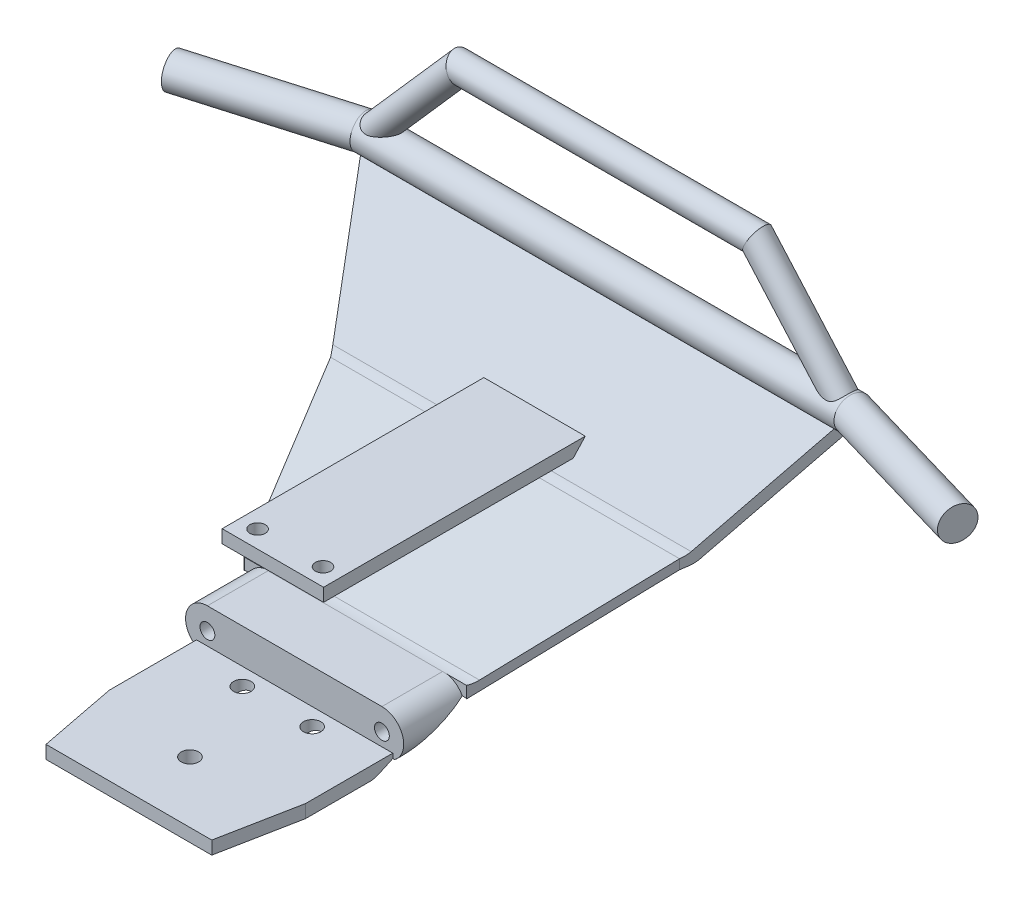
SolidWorks part; units mm, degrees
ref_plane "Front Plane" through (0, 0, 0) normal (0, 0, 1) x (1, 0, 0)
ref_plane "Top Plane" through (0, 0, 0) normal (0, 1, 0) x (1, 0, 0)
ref_plane "Right Plane" through (0, 0, 0) normal (1, 0, 0) x (0, 0, -1)
sketch "Sketch2" plane through (0, 0, 0) normal (1, 0, 0) x (0, 0, -1)
  line L0 (0, 0) -> (32.7095, 0)
  line L1 (34.7929, 0.4547) -> (87.4317, 24.5817)
  line L2 (89.0248, 25.7382) -> (111.3878, 50)
  line L3 (0, 0) -> (0, 3)
  line L4 (0, 3) -> (38, 3)
  line L5 (38, 3) -> (38, 11)
  line L6 (87.8264, 27.389) -> (109.9172, 51.3555)
  line L7 (38, 11) -> (51.9087, 11)
  line L8 (53.992, 11.4547) -> (86.2333, 26.2325)
  line L9 (109.9172, 51.3555) -> (111.3878, 50)
  arc A0 (51.9087, 11) -> (53.992, 11.4547) centre (51.9087, 16) ccw
  arc A1 (86.2333, 26.2325) -> (87.8264, 27.389) centre (84.15, 30.7778) ccw
  arc A2 (87.4317, 24.5817) -> (89.0248, 25.7382) centre (85.3484, 29.127) ccw
  arc A3 (32.7095, 0) -> (34.7929, 0.4547) centre (32.7095, 5) ccw
  point P17 (53, 11)
  point P22 (88.3444, 25)
  point P25 (33.8008, 0)
  dimension "D11" = 5
  dimension "D1" = 8
  dimension "D2" = 3
  dimension "D3" = 60
  dimension "D4" = 34
  dimension "D5" = 2
  dimension "D6" = 2
  dimension "D7" = 25
  dimension "D8" = 50
  dimension "D9" = 38
  dimension "D10" = 15
extrude "Boss-Extrude1" add sketch "Sketch2" along normal mid plane 114
sketch "Sketch18" plane through (0, 3, 0) normal (0, 1, 0) x (1, 0, 0)
  line L0 (0, 0) -> (0, 53.992) construction
  line L1 (57, 0) -> (-57, 0) construction
  line L2 (57, 53.992) -> (-57, 53.992) construction
  circle A0 centre (-8, 34) radius 2
  circle A1 centre (8, 34) radius 2
  circle A2 centre (0, 14) radius 2
  dimension "D3" = 4
  dimension "D4" = 4
  dimension "D5" = 4
  dimension "D1" = 14
  dimension "D2" = 34
  dimension "D6" = 8
  dimension "D7" = 8
extrude "Cut-Extrude3" cut sketch "Sketch18" against normal up to surface (3 mm away) up to face at (0, 0, -16.3548)
ref_plane "Plane2" through (0, 0, -38) normal (0, 0, 1) x (1, 0, 0)
sketch "Sketch19" plane through (0, 0, -38) normal (0, 0, 1) x (1, 0, 0)
  line L0 (0, 0) -> (0, 79.2721) construction
  line L1 (57, 0) -> (-57, 0) construction
  line L2 (-11.625, 30) -> (-11.625, 33)
  line L3 (-11.625, 33) -> (11.625, 33)
  line L4 (57, 0) -> (-57, 0) construction
  line L5 (-11.625, 30) -> (11.625, 30)
  line L8 (11.625, 33) -> (11.625, 30)
  line L9 (-11.625, 31.5) -> (17.3718, 31.5) construction
  point P13 (0, 30)
  dimension "D1" = 23.25
  dimension "D2" = 33
  dimension "D6" = 3
sketch "Sketch23" plane through (0, 0, 0) normal (0, 1, 0) x (1, 0, 0)
  line L0 (19, 0) -> (22.5, 18)
  line L1 (57, 0) -> (-57, 0) construction
  line L2 (22.5, 18) -> (22.5, 38)
  line L3 (22.5, 38) -> (25.5, 38)
  line L4 (25.5, 38) -> (25.5, 51.9087)
  line L5 (25.5, 51.9087) -> (40, 86.2333)
  line L6 (40, 86.2333) -> (57, 111.3878)
  line L7 (57, 111.3878) -> (57, 0)
  line L8 (57, 0) -> (19, 0)
  line L9 (57, 38) -> (-57, 38) construction
  line L10 (57, 51.9087) -> (-57, 51.9087) construction
  line L11 (57, 86.2333) -> (-57, 86.2333) construction
  line L12 (0, 0) -> (0, 127.1657) construction
  line L13 (-57, 0) -> (-19, 0)
  line L14 (-57, 111.3878) -> (-57, 0)
  line L15 (-40, 86.2333) -> (-57, 111.3878)
  line L16 (-25.5, 51.9087) -> (-40, 86.2333)
  line L17 (-25.5, 38) -> (-25.5, 51.9087)
  line L18 (-22.5, 38) -> (-25.5, 38)
  line L19 (-22.5, 18) -> (-22.5, 38)
  line L20 (-19, 0) -> (-22.5, 18)
  point P13 (25.5, 44.9544)
  dimension "D1" = 19
  dimension "D2" = 22.5
  dimension "D3" = 18
  dimension "D4" = 3
  dimension "D5" = 40
extrude "Cut-Extrude5" cut sketch "Sketch23" against normal through all and the other way blind 60
sketch "Sketch24" plane through (0, 0, -38) normal (0, 0, 1) x (1, 0, 0)
  line L0 (19, 0) -> (-19, 0) construction
  line L1 (25.5, 11) -> (-25.5, 11) construction
  line L2 (-20, 11) -> (-25.5, 11)
  line L3 (-25.5, 11) -> (-25.5, 1.9247)
  line L4 (-22.8969, 1.9247) -> (-25.5, 1.9247)
  line L5 (-25.5, 1.9247) -> (-22.5, 1.9247) construction
  line L6 (0, 0) -> (0, 14.7808) construction
  line L7 (22.8969, 1.9247) -> (25.5, 1.9247)
  line L8 (25.5, 11) -> (25.5, 1.9247)
  line L9 (20, 11) -> (25.5, 11)
  circle A0 centre (-20, 6) radius 1.7
  arc A1 (20, 11) -> (22.8969, 1.9247) centre (20, 6) cw
  arc A2 (-20, 11) -> (-22.8969, 1.9247) centre (-20, 6) ccw
  circle A3 centre (20, 6) radius 1.7
  dimension "D1" = 20
  dimension "D2" = 3.4
  dimension "D3" = 6
extrude "Cut-Extrude6" cut sketch "Sketch24" against normal blind 14
sketch3d "3DSketch1"
  line L0 (-90, 51.35, -100) -> (-56.0061, 51.3555, -109.9172)
  line L1 (-56.0061, 51.3555, -109.9172) -> (56.0061, 51.3555, -109.9172)
  line L2 (56.0061, 51.3555, -109.9172) -> (90, 51.35, -100)
  point P0 (-90, 51.35, -100)
  point P1 (-56.0061, 51.3555, -109.9172)
  point P2 (56.0061, 51.3555, -109.9172)
  point P4 (90, 51.35, -100)
  point P6 (90, 51.35, -100)
sweep "Sweep1" add path "3DSketch1" circular profile diameter 7.5 parameters "D3"=7.5
sketch3d "3DSketch2"
  line L0 (-56, 50, -110) -> (-34, 75, -110)
  line L1 (-34, 75, -110) -> (34, 75, -110)
  line L2 (34, 75, -110) -> (56, 50, -110)
  point P0 (-56, 50, -110)
  point P1 (56, 50, -110)
  point P2 (34, 75, -110)
  point P5 (-34, 75, -110)
sweep "Sweep2" add path "3DSketch2" circular profile diameter 6 parameters "D3"=6
extrude "Boss-Extrude2" add sketch "Sketch19" against normal up to surface and the other way blind 5 up to face at (0, 37.9936, -97.6011)
sketch "Sketch54" plane through (0, 33, 0) normal (0, 1, 0) x (1, 0, 0)
  line L0 (0, 0) -> (0, 53.992) construction
  line L1 (26.3801, 53.992) -> (-26.3801, 53.992) construction
  line L2 (11.625, 33) -> (-11.625, 33) construction
  circle A0 centre (-7.5, 37) radius 1.75
  circle A1 centre (7.5, 37) radius 1.75
  dimension "D3" = 3.5
  dimension "D1" = 4
  dimension "D2" = 7.5
extrude "Cut-Extrude8" cut sketch "Sketch54" against normal up to next
